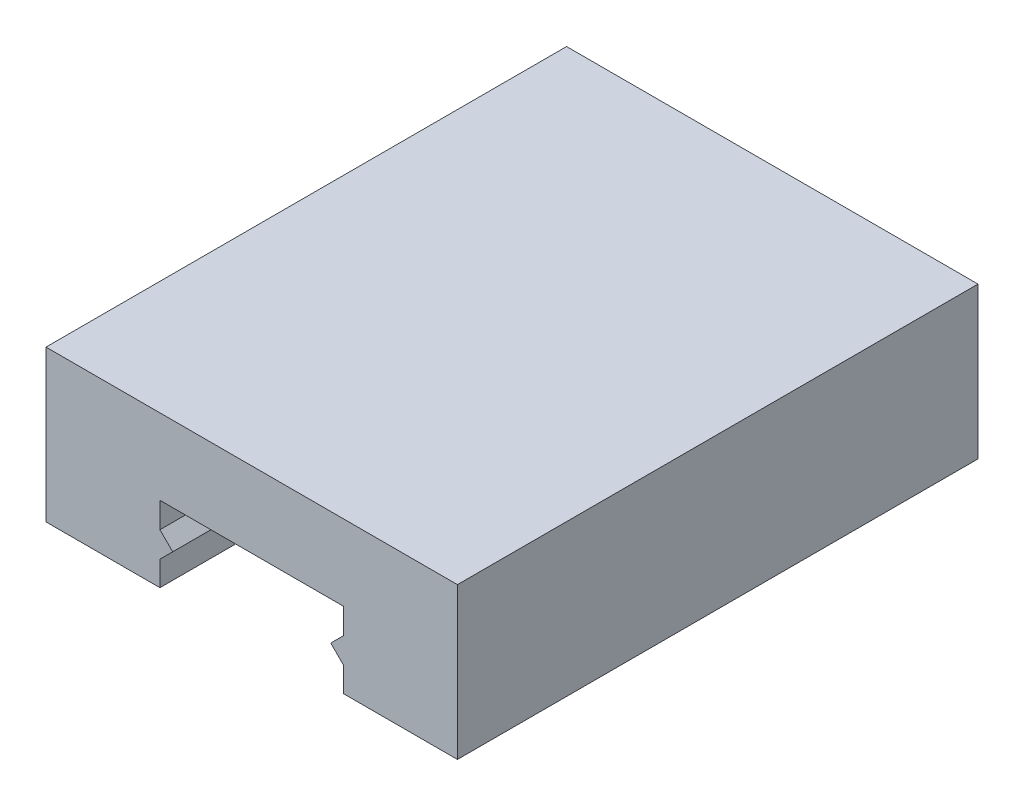
SolidWorks part; units mm, degrees
material "Cast Alloy Steel"
ref_plane "Front Plane" through (0, 0, 0) normal (0, 0, 1) x (1, 0, 0)
ref_plane "Top Plane" through (0, 0, 0) normal (0, 1, 0) x (1, 0, 0)
ref_plane "Right Plane" through (0, 0, 0) normal (1, 0, 0) x (0, 0, -1)
sketch "Sketch1" plane through (0, 0, 0) normal (0, 0, 1) x (1, 0, 0)
  line L28 (-6, 1.6667) -> (-5.1667, 2.5)
  line L29 (-5.1667, 2.5) -> (-6, 3.3333)
  line L30 (-6, 3.3333) -> (-6, 5)
  line L31 (-6, 5) -> (6, 5)
  line L32 (6, 5) -> (6, 3.3333)
  line L33 (6, 3.3333) -> (5.1667, 2.5)
  line L34 (5.1667, 2.5) -> (6, 1.6667)
  line L35 (6, 1.6667) -> (6, 0.05)
  line L36 (6, 0.05) -> (13.45, 0.05)
  line L37 (13.45, 0.05) -> (13.45, 9.95)
  line L38 (13.45, 9.95) -> (-13.45, 9.95)
  line L39 (-13.45, 9.95) -> (-13.45, 0.05)
  line L40 (-13.45, 0.05) -> (-6, 0.05)
  line L41 (-6, 0.05) -> (-6, 1.6667)
extrude "Boss-Extrude1" add sketch "Sketch1" along normal blind 34.036
sketch "Sketch2" plane through (0, 9.95, 0) normal (0, 1, 0) x (1, 0, 0)
  line L0 (-13.45, -34.036) -> (13.45, 0) construction
  line L1 (13.45, -34.036) -> (-13.45, 0) construction
  line L4 (13.45, 0) -> (-13.45, 0)
  line L5 (-13.45, 0) -> (-13.45, -34.036)
  line L6 (-13.45, -34.036) -> (13.45, -34.036)
  line L7 (13.45, -34.036) -> (13.45, 0)
  line L8 (13.45, 0) -> (-13.45, 0) construction
  line L9 (-13.45, 0) -> (-13.45, -34.036) construction
  line L10 (-13.45, -34.036) -> (13.45, -34.036) construction
  line L11 (13.45, -34.036) -> (13.45, 0) construction
  point P2 (0, -17.018)
  dimension "D1" = 0
